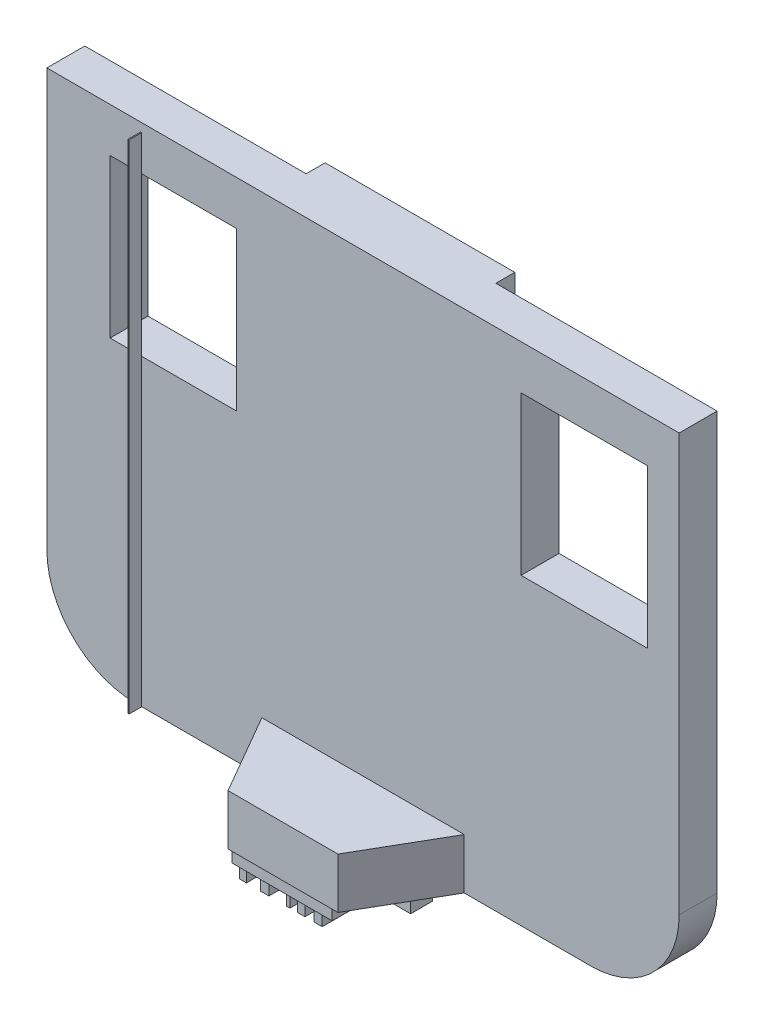
SolidWorks part; units mm, degrees
ref_plane "Front Plane" through (0, 0, 0) normal (0, 0, 1) x (1, 0, 0)
ref_plane "Top Plane" through (0, 0, 0) normal (0, 1, 0) x (1, 0, 0)
ref_plane "Right Plane" through (0, 0, 0) normal (1, 0, 0) x (0, 0, -1)
sketch "Sketch1" plane through (0, 0, 0) normal (0, 0, 1) x (1, 0, 0)
  line L1 (0, 0) -> (127, 0)
  line L2 (0, 0) -> (0, 101.6)
  line L3 (0, 101.6) -> (127, 101.6)
  line L4 (127, 0) -> (127, 101.6)
  dimension "D1" = 127
  dimension "D2" = 101.6
extrude "Boss-Extrude1" add sketch "Sketch1" along normal blind 7.62
sketch "Sketch3" plane through (0, 0, 0) normal (0, 0, -1) x (-1, 0, 0)
  line L0 (-127, 101.6) -> (0, 101.6) construction
  line L1 (-82.55, 101.6) -> (-44.45, 101.6)
  line L2 (-82.55, 101.6) -> (-82.55, 0)
  line L3 (-82.55, 0) -> (-44.45, 0)
  line L4 (-44.45, 101.6) -> (-44.45, 0)
  line L5 (0, 0) -> (-127, 0) construction
  line L6 (-127, 0) -> (-127, 101.6) construction
  dimension "D1" = 38.1
  dimension "D2" = 44.45
extrude "Boss-Extrude2" add sketch "Sketch3" along normal blind 3.81
sketch "Sketch4" plane through (0, 0, 0) normal (0, 0, -1) x (-1, 0, 0)
  line L0 (-127, 0) -> (-127, 101.6) construction
  line L1 (-38.1, 92.71) -> (-12.7, 92.71)
  line L2 (-38.1, 92.71) -> (-38.1, 60.96)
  line L3 (-38.1, 60.96) -> (-12.7, 60.96)
  line L4 (-12.7, 92.71) -> (-12.7, 60.96)
  line L5 (-120.65, 92.71) -> (-95.25, 92.71)
  line L6 (-120.65, 92.71) -> (-120.65, 60.96)
  line L7 (-120.65, 60.96) -> (-95.25, 60.96)
  line L8 (-95.25, 92.71) -> (-95.25, 60.96)
  line L9 (-127, 101.6) -> (-82.55, 101.6) construction
  line L10 (-44.45, 101.6) -> (0, 101.6) construction
  dimension "D1" = 25.4
  dimension "D2" = 31.75
  dimension "D3" = 31.75
  dimension "D4" = 25.4
  dimension "D5" = 107.95
  dimension "D6" = 6.35
  dimension "D7" = 8.89
  dimension "D8" = 8.89
extrude "Cut-Extrude1" cut sketch "Sketch4" against normal blind 7.62
fillet "Fillet1" radius 17.78 2 edges at (127, 0, 3.81) (0, 0, 3.81)
sketch "Sketch5" plane through (0, 0, 0) normal (0, -1, 0) x (1, 0, 0)
  line L0 (43.18, 7.62) -> (52.463, 23.6987)
  line L1 (17.78, 7.62) -> (109.22, 7.62) construction
  line L2 (52.463, 23.6987) -> (74.537, 23.6987)
  line L3 (74.537, 23.6987) -> (83.82, 7.62)
  line L4 (43.18, 7.62) -> (83.82, 7.62)
  dimension "D1" = 25.4
  dimension "D2" = 25.4
  dimension "D3" = 60
  dimension "D4" = 60
extrude "Boss-Extrude3" add sketch "Sketch5" against normal blind 10.16
sketch "Sketch6" plane through (0, 0, 0) normal (0, -1, 0) x (1, 0, 0)
  line L0 (51.6682, 11.5503) -> (51.6682, 7.1559)
  line L1 (51.6682, 7.1559) -> (76.9898, 7.1559)
  line L2 (76.9898, 11.5503) -> (51.6682, 11.5503)
  line L3 (76.9898, 7.1559) -> (76.9898, 11.5503)
  line L4 (64.329, 11.5503) -> (64.329, 7.1559)
  line L5 (53.733, 22.6805) -> (53.733, 15.5965)
  line L6 (53.733, 15.5965) -> (72.5736, 15.5965)
  line L7 (72.5736, 15.5965) -> (72.5736, 22.6805)
  line L8 (72.5736, 22.6805) -> (53.733, 22.6805)
  line L9 (55.1348, 15.5965) -> (55.1348, 22.6805)
  line L10 (55.1348, 22.6805) -> (57.9986, 22.6805)
  line L11 (57.9986, 22.6805) -> (57.9986, 15.5965)
  line L12 (57.9986, 15.5965) -> (59.6565, 15.5965)
  line L13 (59.6565, 15.5965) -> (59.6565, 22.6805)
  line L14 (59.6565, 22.6805) -> (63.1533, 22.6805)
  line L15 (63.1533, 22.6805) -> (63.1533, 15.5965)
  line L16 (63.1533, 15.5965) -> (63.8768, 15.5965)
  line L17 (63.8768, 15.5965) -> (63.8768, 22.6805)
  line L18 (63.8768, 22.6805) -> (66.8913, 22.6805)
  line L19 (66.8913, 22.6805) -> (66.8913, 15.5965)
  line L20 (66.8913, 15.5965) -> (68.7, 15.5965)
  line L21 (68.7, 15.5965) -> (68.7, 22.6805)
  line L22 (68.7, 22.6805) -> (70.3579, 22.6805)
  line L23 (70.3579, 22.6805) -> (70.3579, 15.5965)
  line L24 (70.3579, 15.5965) -> (65.3841, 15.5965)
  line L25 (65.3841, 15.5965) -> (65.3841, 22.6805)
  dimension "D1" = 1.27
extrude "Boss-Extrude4" add sketch "Sketch6" along normal blind 5.08 contours L6 L9 L8 L5 | L6 L13 L8 L11 | L6 L17 L8 L15 | L25 L6 L19 L8 | L23 L8 L21 L6 | L4 L2 L0 L1 | L2 L4 L1 L3
sketch "Sketch7" plane through (0, -5.08, 0) normal (0, -1, 0) x (1, 0, 0)
  line L0 (64.329, 7.1559) -> (64.329, 11.5503)
  line L1 (51.6682, 7.1559) -> (76.9898, 7.1559) construction
  line L2 (76.9898, 11.5503) -> (51.6682, 11.5503) construction
  line L3 (64.329, 11.5503) -> (63.3398, 11.5503)
  line L4 (63.3398, 11.5503) -> (63.3398, 7.1559)
  line L5 (51.6682, 7.1559) -> (76.9898, 7.1559) construction
  line L6 (63.3398, 7.1559) -> (65.5485, 7.1559)
  line L7 (65.5485, 7.1559) -> (65.5485, 11.5503)
  line L8 (65.5485, 11.5503) -> (63.3398, 11.5503)
  line M1 (51.6682, 7.1559) -> (76.9898, 7.1559)
  line M3 (76.9898, 11.5503) -> (51.6682, 11.5503)
extrude "Cut-Extrude2" cut sketch "Sketch7" against normal blind 5.08 contours L4 L0 M3 M1 | L7 L0 M1 M3
sketch "Sketch8" plane through (0, 0, 0) normal (0, -1, 0) x (1, 0, 0)
  line L1 (52.7513, 23.1897) -> (72.878, 23.1897)
  line L2 (52.7513, 23.1897) -> (52.7513, 15.2934)
  line L3 (52.7513, 15.2934) -> (72.878, 15.2934)
  line L4 (72.878, 23.1897) -> (72.878, 15.2934)
extrude "Boss-Extrude5" add sketch "Sketch8" along normal blind 2.54
sketch "Sketch9" plane through (0, 0, 7.62) normal (0, 0, 1) x (1, 0, 0)
  line L1 (19.05, 99.8802) -> (18.8364, 99.8802)
  line L2 (19.05, 99.8802) -> (19.05, 0)
  line L3 (19.05, 0) -> (18.8364, 0)
  line L4 (18.8364, 99.8802) -> (18.8364, 0)
  line L5 (0, 101.6) -> (0, 17.78) construction
  dimension "D1" = 0.2136
  dimension "D2" = 19.05
extrude "Boss-Extrude6" add sketch "Sketch9" along normal blind 2.54
